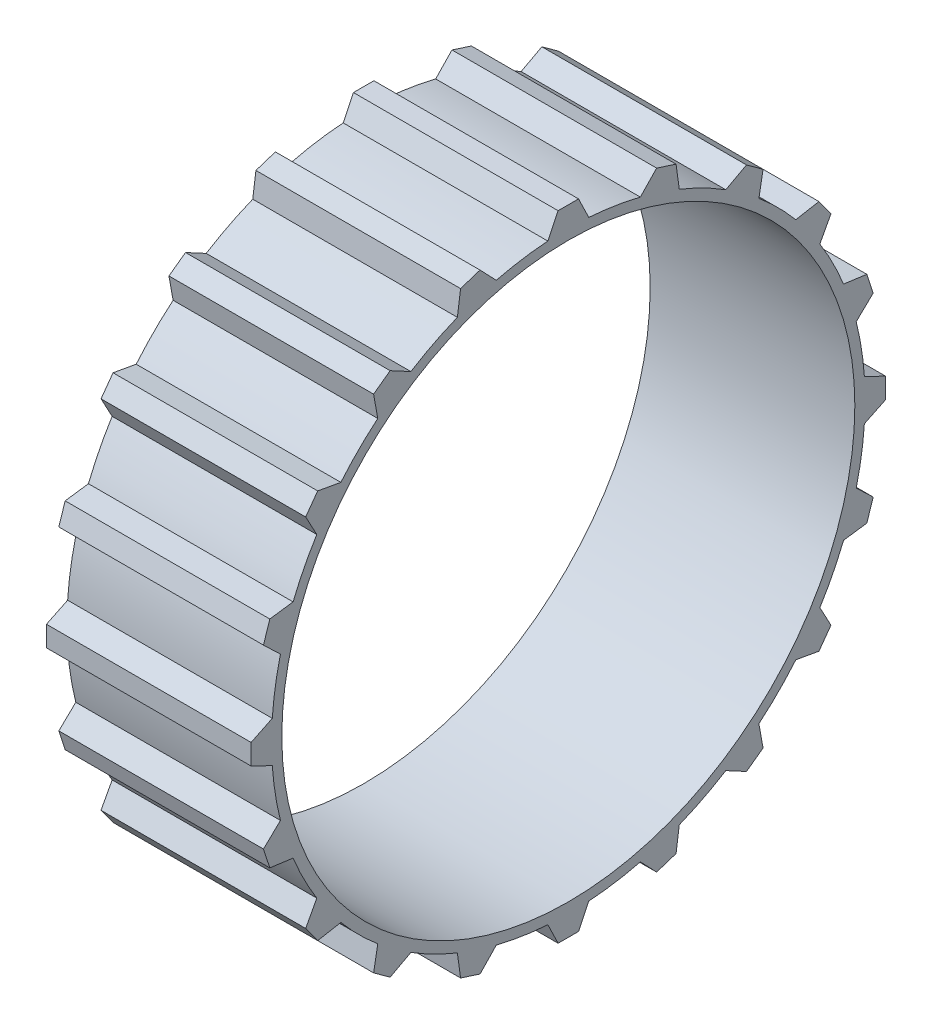
SolidWorks part; units mm, degrees
ref_plane "Front Plane" through (0, 0, 0) normal (0, 0, 1) x (1, 0, 0)
ref_plane "Top Plane" through (0, 0, 0) normal (0, 1, 0) x (1, 0, 0)
ref_plane "Right Plane" through (0, 0, 0) normal (1, 0, 0) x (0, 0, -1)
sketch "Sketch1" plane through (13.8767, 0, 0) normal (1, 0, 0) x (0, 0, -1)
  circle A0 centre (67.4694, -50.6615) radius 28
  circle A2 centre (67.4694, -50.6615) radius 29
  dimension "D1" = 1
extrude "Boss-Extrude1" add sketch "Sketch1" against normal up to surface (20 mm away)
sketch "Sketch2" plane through (13.8767, 0, 0) normal (1, 0, 0) x (0, 0, -1)
  line L0 (65.4694, -21.7306) -> (66.4694, -19.6615)
  line L1 (66.4694, -19.6615) -> (68.4694, -19.6615)
  line L2 (68.4694, -19.6615) -> (69.4694, -21.7306)
  line L3 (67.4694, -22.6615) -> (67.4694, -78.6615) construction
  circle A0 centre (67.4694, -50.6615) radius 29 construction
  circle A1 centre (67.4694, -50.6615) radius 28 construction
  circle A3 centre (67.4694, -50.6615) radius 29
  arc A4 (65.4694, -21.7306) -> (69.4694, -21.7306) centre (67.4694, -50.6615) ccw
  circle M6 centre (67.4694, -50.6615) radius 29
  dimension "D1" = 4
  dimension "D2" = 3
  dimension "D3" = 2
  dimension "D4" = 0
extrude "Boss-Extrude2" add sketch "Sketch2" against normal through all contours L2 L1 L0 M6
pattern_circular "CirPattern1" count 20 over 360 about axis through (0, -50.6615, -67.4694) along (1, 0, 0) of "Boss-Extrude2"
